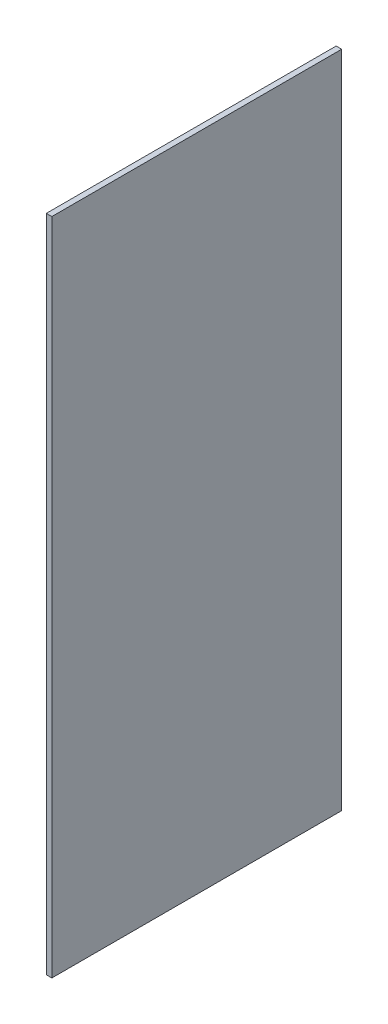
SolidWorks part; units mm, degrees
ref_plane "Front Plane" through (0, 0, 0) normal (0, 0, 1) x (1, 0, 0)
ref_plane "Top Plane" through (0, 0, 0) normal (0, 1, 0) x (1, 0, 0)
ref_plane "Right Plane" through (0, 0, 0) normal (1, 0, 0) x (0, 0, -1)
sketch "Sketch1" plane through (0, 0, 0) normal (1, 0, 0) x (0, 0, -1)
  line L1 (-31.75, -72.2313) -> (31.75, -72.2313)
  line L2 (-31.75, -72.2313) -> (-31.75, 72.2313)
  line L3 (-31.75, 72.2313) -> (31.75, 72.2313)
  line L4 (31.75, -72.2313) -> (31.75, 72.2313)
  line L5 (-31.75, -72.2313) -> (31.75, 72.2313) construction
  line L6 (-31.75, 72.2313) -> (31.75, -72.2313) construction
  point P0 (0, 0)
  dimension "D1" = 144.4625
  dimension "D2" = 63.5
extrude "Boss-Extrude1" add sketch "Sketch1" along normal blind 1.2141
